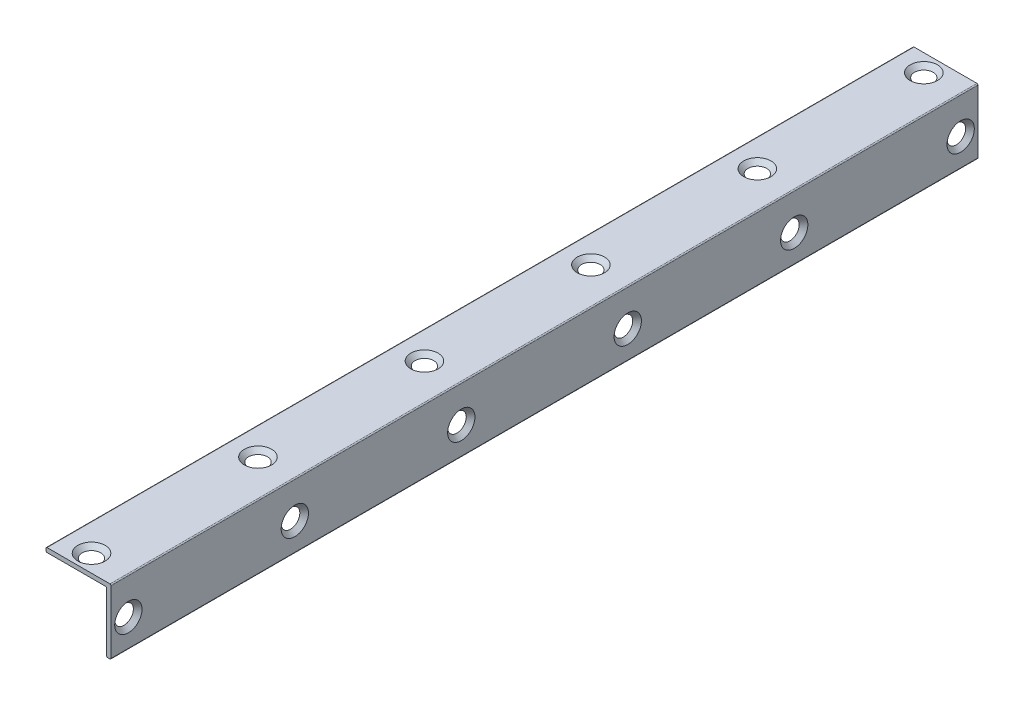
SolidWorks part; units mm, degrees
ref_plane "Front Plane" through (0, 0, 0) normal (0, 0, 1) x (1, 0, 0)
ref_plane "Top Plane" through (0, 0, 0) normal (0, 1, 0) x (1, 0, 0)
ref_plane "Right Plane" through (0, 0, 0) normal (1, 0, 0) x (0, 0, -1)
sketch "Sketch1" plane through (0, 0, 0) normal (0, 0, 1) x (1, 0, 0)
  line L0 (0, 0) -> (0, 15)
  line L1 (0, 15) -> (-15, 15)
  line L2 (-15, 15) -> (-15, 14)
  line L3 (-15, 14) -> (-1, 14)
  line L4 (-1, 14) -> (-1, 0)
  line L5 (-1, 0) -> (0, 0)
extrude "Extrude1" add sketch "Sketch1" along normal blind 200
fillet "Fillet1" radius 0.25 5 edges at (-1, 0, 100) (0, 0, 100) (0, 15, 100) (-15, 15, 100) (-15, 14, 100)
sketch "Sketch2" plane through (0, 0, 0) normal (1, 0, 0) x (0, 0, -1)
  line L0 (-4, 14.75) -> (-4, 0.25) construction
  line L1 (0, 14.75) -> (-200, 14.75) construction
  line L2 (-200, 0.25) -> (0, 0.25) construction
  point P6 (-4, 6.5)
hole_wizard "CSK for M3 Countersunk Flat Head Screw1" positions "3DSketch1" profile "Sketch3" countersink size "M3" standard "DIN" end condition up to next
sketch3d "3DSketch1"
  point P0 (0, 6.5, 4)
sketch "Sketch3" plane through (0, 6.5, 4) normal (0, 1, 0) x (0, 0, -1)
  line L0 (0, 0) -> (0, 1.001)
  line L1 (0, 1.001) -> (1.7, 1.001)
  line L2 (1.7, 1.001) -> (1.7, 1.45)
  line L3 (1.7, 1.45) -> (3.15, 0)
  line L5 (3.15, 0) -> (0, 0)
  line L6 (-1.7, 1.45) -> (-3.15, 0) construction
  line L11 (0, -6.35) -> (0, 107.95) construction
  dimension "Thru Hole Dia." = 3.4
  dimension "Thru Hole Depth" = 1.001
  dimension "Near C'Sink Dia." = 6.3
  dimension "Near C'Sink Angle" = 90
pattern_linear "LPattern1" count 6 spacing 38.4 along (0, 0, 1) of "CSK for M3 Countersunk Flat Head Screw1"
sketch "Sketch4" plane through (0, 15, 0) normal (0, 1, 0) x (1, 0, 0)
  line L0 (-14.75, -4) -> (-0.25, -4) construction
  line L1 (-14.75, 0) -> (-14.75, -200) construction
  line L2 (-0.25, -200) -> (-0.25, 0) construction
  point P6 (-8.5, -4)
hole_wizard "CSK for M3 Countersunk Flat Head Screw2" positions "3DSketch2" profile "Sketch5" countersink size "M3" standard "DIN" end condition up to next
sketch3d "3DSketch2"
  point P0 (-8.5, 15, 4)
sketch "Sketch5" plane through (-8.5, 15, 4) normal (1, 0, 0) x (0, 0, 1)
  line L0 (0, 0) -> (0, 1.001)
  line L1 (0, 1.001) -> (1.7, 1.001)
  line L2 (1.7, 1.001) -> (1.7, 1.45)
  line L3 (1.7, 1.45) -> (3.15, 0)
  line L5 (3.15, 0) -> (0, 0)
  line L6 (-1.7, 1.45) -> (-3.15, 0) construction
  line L11 (0, -6.35) -> (0, 107.95) construction
  dimension "Thru Hole Dia." = 3.4
  dimension "Thru Hole Depth" = 1.001
  dimension "Near C'Sink Dia." = 6.3
  dimension "Near C'Sink Angle" = 90
pattern_linear "LPattern2" count 6 spacing 38.4 along (0, 0, 1) of "CSK for M3 Countersunk Flat Head Screw2"
